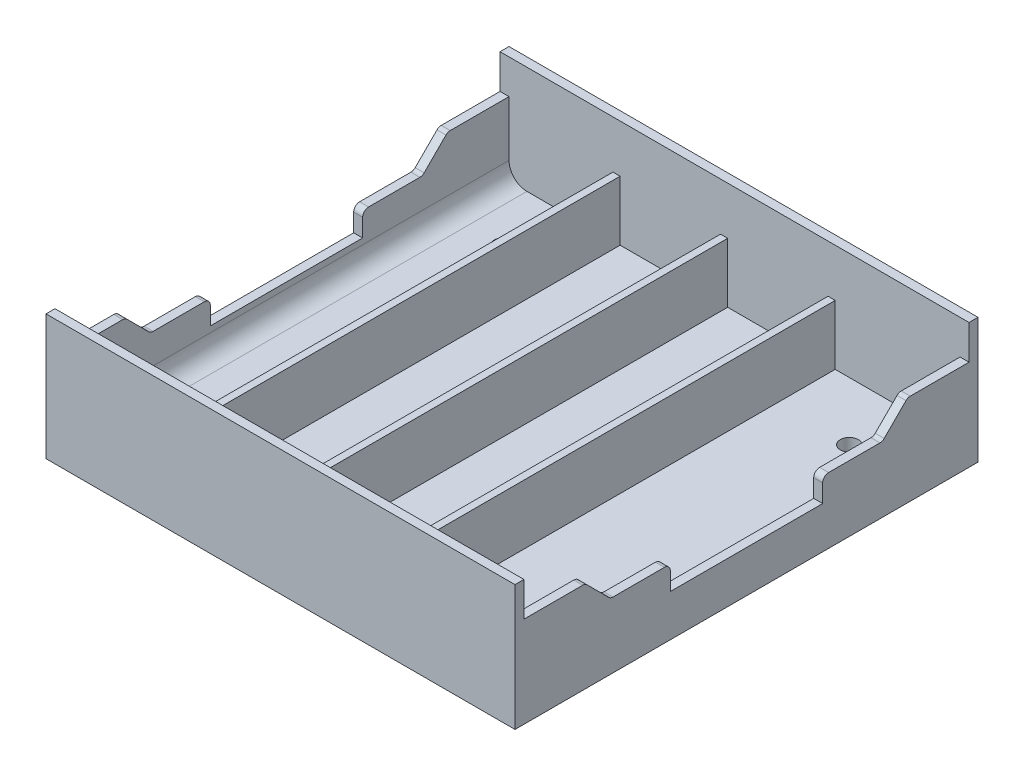
SolidWorks part; units mm, degrees
ref_plane "Front Plane" through (0, 0, 0) normal (0, 0, 1) x (1, 0, 0)
ref_plane "Top Plane" through (0, 0, 0) normal (0, 1, 0) x (1, 0, 0)
ref_plane "Right Plane" through (0, 0, 0) normal (1, 0, 0) x (0, 0, -1)
sketch "Sketch1" plane through (0, 0, 0) normal (0, 1, 0) x (1, 0, 0)
  line L1 (0, 0) -> (78.5, 0)
  line L2 (0, 0) -> (0, 77.5)
  line L3 (0, 77.5) -> (78.5, 77.5)
  line L4 (78.5, 0) -> (78.5, 77.5)
  dimension "D1" = 78.5
  dimension "D2" = 77.5
extrude "Boss-Extrude1" add sketch "Sketch1" along normal blind 21
sketch "Sketch2" plane through (0, 21, 0) normal (0, 1, 0) x (1, 0, 0)
  line L8 (1.5, 76) -> (1.5, 1.5)
  line L9 (1.5, 1.5) -> (77, 1.5)
  line L10 (77, 1.5) -> (77, 76)
  line L11 (77, 76) -> (1.5, 76)
  line L12 (1.5, 76) -> (1.5, 1.5)
  line L13 (1.5, 1.5) -> (77, 1.5)
  line L14 (77, 1.5) -> (77, 76)
  line L15 (77, 76) -> (1.5, 76)
  dimension "D1" = 1.5
extrude "Cut-Extrude1" cut sketch "Sketch2" against normal blind 18
sketch "Sketch3" plane through (78.5, 0, 0) normal (1, 0, 0) x (0, 0, -1)
  line L0 (38.75, 21) -> (38.75, 0) construction
  line L1 (0, 21) -> (77.5, 21) construction
  line L2 (0, 0) -> (77.5, 0) construction
  line L3 (26, 7) -> (51.5, 7)
  line L4 (26, 7) -> (26, 10)
  line L5 (25, 11) -> (16.4142, 11)
  line L6 (15.7071, 11.2929) -> (12.0503, 14.9497)
  line L7 (11.3431, 15.2426) -> (1.5, 15.2426)
  line L8 (0, 21) -> (0, 0) construction
  line L9 (1.5, 15.2426) -> (1.5, 21)
  line L10 (76, 15.2426) -> (76, 21)
  line L11 (66.1569, 15.2426) -> (76, 15.2426)
  line L12 (61.7929, 11.2929) -> (65.4497, 14.9497)
  line L13 (52.5, 11) -> (61.0858, 11)
  line L14 (51.5, 7) -> (51.5, 10)
  line L15 (1.5, 21) -> (76, 21)
  arc A0 (16.4142, 11) -> (15.7071, 11.2929) centre (16.4142, 12) cw
  arc A1 (12.0503, 14.9497) -> (11.3431, 15.2426) centre (11.3431, 14.2426) ccw
  arc A2 (26, 10) -> (25, 11) centre (25, 10) ccw
  arc A3 (65.4497, 14.9497) -> (66.1569, 15.2426) centre (66.1569, 14.2426) cw
  arc A4 (61.0858, 11) -> (61.7929, 11.2929) centre (61.0858, 12) ccw
  arc A5 (51.5, 10) -> (52.5, 11) centre (52.5, 10) cw
  point P17 (16, 11)
  point P20 (11.7574, 15.2426)
  point P23 (26, 11)
  point P36 (38.75, 7)
  dimension "D9" = 1
  dimension "D1" = 12.75
  dimension "D3" = 7
  dimension "D4" = 4
  dimension "D5" = 10
  dimension "D6" = 45
  dimension "D7" = 6
  dimension "D8" = 1.5
extrude "Cut-Extrude2" cut sketch "Sketch3" against normal through all
ref_plane "Plane1" through (0, 13, 0) normal (0, 1, 0) x (1, 0, 0)
sketch "Sketch5" plane through (0, 13, 0) normal (0, 1, 0) x (1, 0, 0)
  line L0 (19.5, 1.5) -> (19.5, 76)
  line L1 (0, 1.5) -> (78.5, 1.5) construction
  line L2 (77, 76) -> (1.5, 76) construction
  line L3 (37.5, 1.5) -> (37.5, 76)
  line L4 (1.5, 1.5) -> (77, 1.5) construction
  line L5 (78.5, 76) -> (0, 76) construction
  line L6 (55.5, 1.5) -> (55.5, 76)
  line L7 (1.5, 51.5) -> (1.5, 26) construction
  dimension "D1" = 18
  dimension "D2" = 18
  dimension "D3" = 18
rib "Rib2" sketch "Sketch5" sketch "Sketch5" thickness 1.2 extrusion direction normal to sketch draft on no parameters "D1"=1.2
fillet "Fillet1" radius 3 2 edges at (77, 3, -38.75) (1.5, 3, -38.75)
sketch "Sketch6" plane through (0, 0, 0) normal (0, -1, 0) x (-1, 0, 0)
  line L0 (-78.5, 38.75) -> (0, 38.75) construction
  line L1 (-78.5, 0) -> (-78.5, 77.5) construction
  line L2 (0, 77.5) -> (0, 0) construction
  line L3 (-39.25, 0) -> (-39.25, 77.5) construction
  line L4 (0, 0) -> (-78.5, 0) construction
  line L5 (-78.5, 77.5) -> (0, 77.5) construction
  line L6 (-70.1991, 11.25) -> (0, 11.25) construction
  line L7 (-68.2, 11.25) -> (-68.2, 66.25) construction
  point P16 (-48.9, 11.25)
  point P17 (-68.2, 11.25)
  point P18 (-29.6, 11.25)
  point P19 (-10.3, 11.25)
  point P23 (-10.3, 66.25)
  point P24 (-29.6, 66.25)
  point P25 (-48.9, 66.25)
  point P26 (-68.2, 66.25)
  dimension "D1" = 27.5
  dimension "D2" = 28.95
  dimension "D3" = 19.3
  dimension "D4" = 19.3
  dimension "D5" = 19.3
hole_wizard "Ø3.0mm Dowel Hole1" positions "Sketch7" profile "Sketch8" hole size "Ø3.0" standard "ANSI Metric" end condition through all
sketch "Sketch7" plane through (0, 0, 0) normal (0, -1, 0) x (-1, 0, 0)
  point P0 (-68.2, 11.25)
  point P3 (-48.9, 11.25)
  point P6 (-29.6, 11.25)
  point P9 (-10.3, 11.25)
  point P12 (-10.3, 66.25)
  point P15 (-29.6, 66.25)
  point P18 (-48.9, 66.25)
  point P21 (-68.2, 66.25)
  point P24 (-68.2, 66.25)
sketch "Sketch8" plane through (68.2, 0, -11.25) normal (1, 0, 0) x (0, 0, -1)
  line L0 (0, 0) -> (0, 21)
  line L1 (0, 21) -> (1.5, 21)
  line L2 (1.5, 21) -> (1.5, 0)
  line L5 (1.5, 0) -> (0, 0)
  line L11 (0, -6.35) -> (0, 107.95) construction
  dimension "Thru Hole Dia." = 3
  dimension "Thru Hole Depth" = 21
